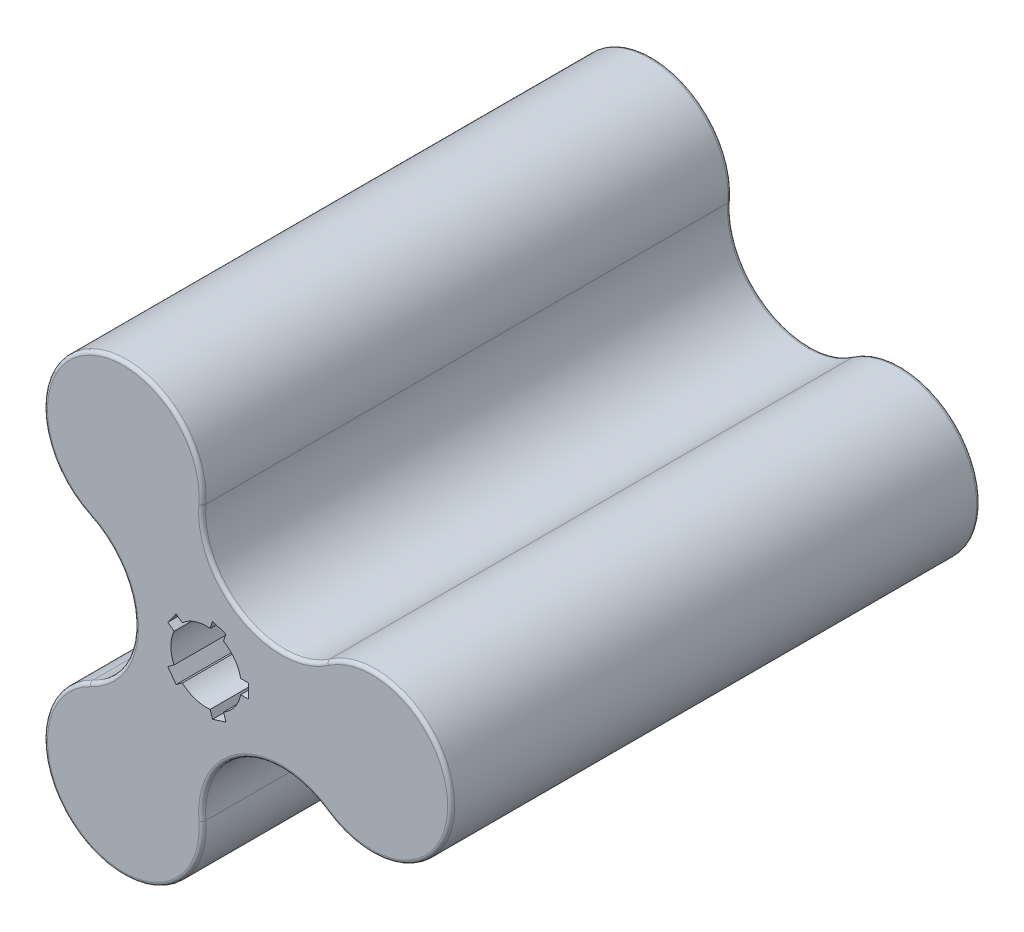
SolidWorks part; units mm, degrees
ref_plane "Front Plane" through (0, 0, 0) normal (0, 0, 1) x (1, 0, 0)
ref_plane "Top Plane" through (0, 0, 0) normal (0, 1, 0) x (1, 0, 0)
ref_plane "Right Plane" through (0, 0, 0) normal (1, 0, 0) x (0, 0, -1)
sketch "Sketch1" plane through (0, 0, 0) normal (0, 0, 1) x (1, 0, 0)
  line L0 (0, 0) -> (20038.6462, 0) construction
  line L1 (0, 0) -> (0, 20038.6462) construction
  line L2 (0.57, -8.2265) -> (1.8061, -12.0307)
  line L3 (8, -2) -> (12, -2)
  line L4 (8, -2) -> (8, 2)
  line L5 (8, 2) -> (12, 2)
  line L6 (12, -2) -> (12, 2)
  line L7 (8, -2) -> (12, 2) construction
  line L8 (8, 2) -> (12, -2) construction
  line L9 (1.8061, -12.0307) -> (5.6103, -10.7946)
  line L10 (4.3742, -6.9904) -> (5.6103, -10.7946)
  line L11 (0.57, -8.2265) -> (4.3742, -6.9904)
  line L12 (-7.6477, -3.0842) -> (-10.8838, -5.4354)
  line L13 (-10.8838, -5.4354) -> (-8.5326, -8.6715)
  line L14 (-5.2966, -6.3203) -> (-8.5326, -8.6715)
  line L15 (-7.6477, -3.0842) -> (-5.2966, -6.3203)
  line L16 (-5.2966, 6.3203) -> (-8.5326, 8.6715)
  line L17 (-8.5326, 8.6715) -> (-10.8838, 5.4354)
  line L18 (-7.6477, 3.0842) -> (-10.8838, 5.4354)
  line L19 (-5.2966, 6.3203) -> (-7.6477, 3.0842)
  line L20 (4.3742, 6.9904) -> (5.6103, 10.7946)
  line L21 (5.6103, 10.7946) -> (1.8061, 12.0307)
  line L22 (0.57, 8.2265) -> (1.8061, 12.0307)
  line L23 (4.3742, 6.9904) -> (0.57, 8.2265)
  circle A0 centre (0, 0) radius 10
  circle A1 centre (47, 0) radius 22.5
  circle A2 centre (-23.5, -40.7032) radius 22.5
  circle A3 centre (-23.5, 40.7032) radius 22.5
  arc A4 (-1.0775, 38.8368) -> (34.1725, 18.4852) centre (21.3449, 36.9705) ccw
  arc A5 (34.1725, -18.4852) -> (-1.0775, -38.8368) centre (21.3449, -36.9705) ccw
  arc A6 (-33.0949, -20.3516) -> (-33.0949, 20.3516) centre (-42.6898, 0) ccw
  point P15 (0, 0)
  point P18 (0, 0)
  point P19 (10, 0)
  point P25 (0, 0)
  point P48 (0, 0)
  dimension "D1" = 20
  dimension "D2" = 45
  dimension "D5" = 22.5
  dimension "D3" = 47
  dimension "D7" = 21.3449
  dimension "D8" = 4
  dimension "D9" = 4
  dimension "D10" = 5
  dimension "D4" = 3
  dimension "D6" = 3
extrude "Boss-Extrude1" add sketch "Sketch1" along normal mid plane 150 contours A3 | A1 | A2 | A6 A2 A5 A1 A4 A3 A0 L5 L6 L3 L10 L9 L2 L14 L13 L12 L18 L17 L16 L22 L21 L20
fillet "Fillet1" radius 1 12 edges at (10.0949, 17.4849, -75) (10.0949, 17.4849, 75) (69.5, 0, -75) (69.5, 0, 75) (10.0949, -17.4849, -75) (10.0949, -17.4849, 75) (-34.75, -60.1888, -75) (-34.75, -60.1888, 75) (-20.1898, 0, -75) (-20.1898, 0, 75) (-34.75, 60.1888, -75) (-34.75, 60.1888, 75)
